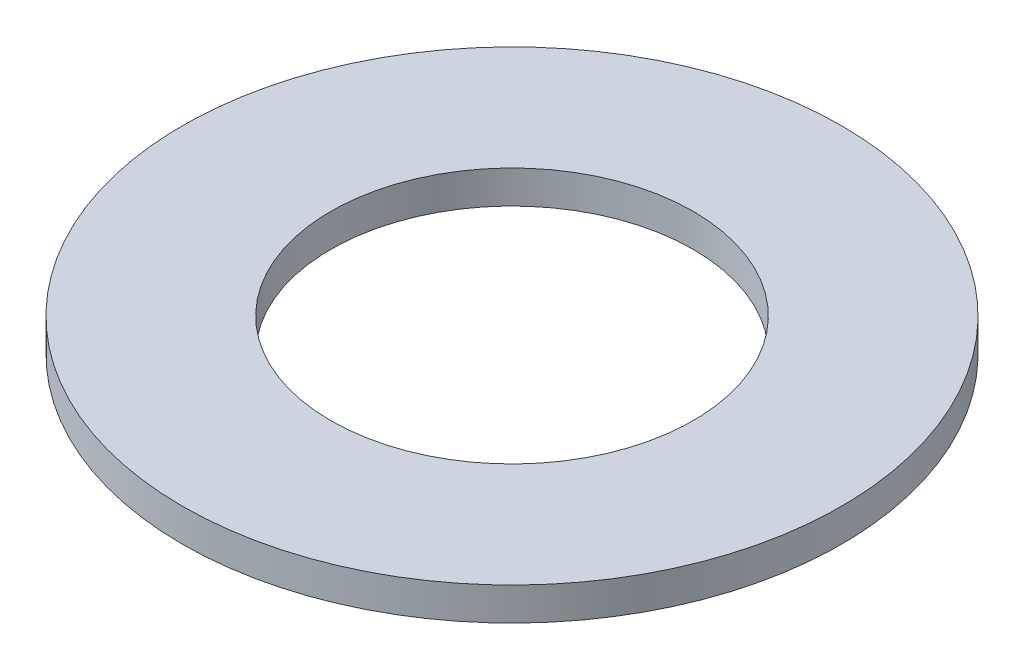
SolidWorks part; units mm, degrees
ref_plane "Alzado" through (0, 0, 0) normal (0, 0, 1) x (1, 0, 0)
ref_plane "Planta" through (0, 0, 0) normal (0, 1, 0) x (1, 0, 0)
ref_plane "Vista lateral" through (0, 0, 0) normal (1, 0, 0) x (0, 0, -1)
sketch "Croquis1" plane through (0, 0, 0) normal (0, 1, 0) x (1, 0, 0)
  circle A0 centre (0, 0) radius 10
  circle A1 centre (0, 0) radius 5.5
  dimension "D1" = 20
  dimension "D2" = 11
extrude "Saliente-Extruir1" add sketch "Croquis1" along normal blind 1
